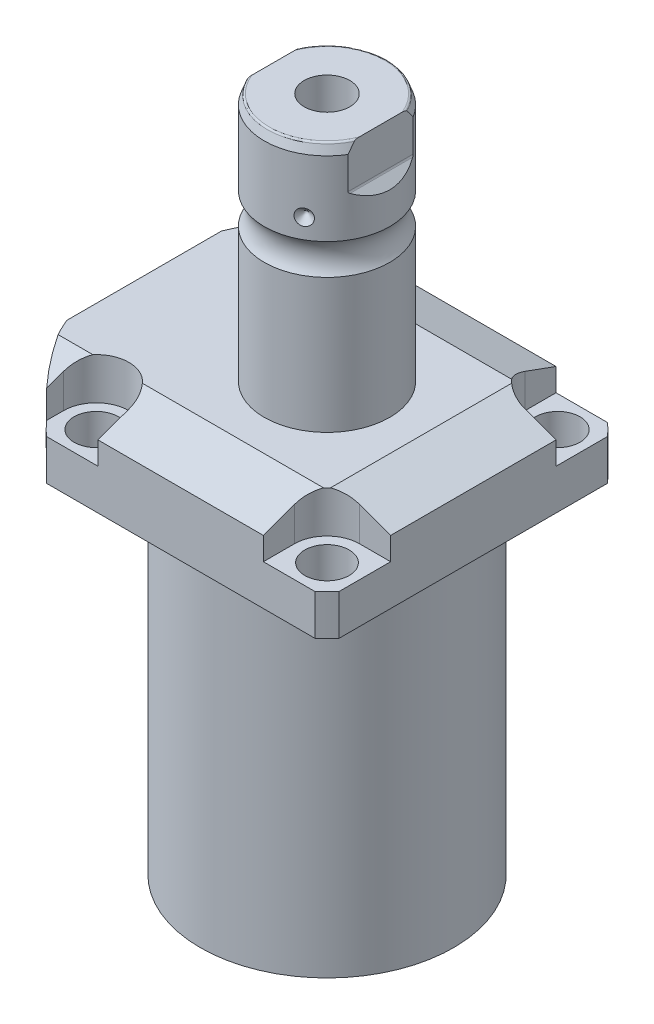
SolidWorks part; units mm, degrees
material "Alloy Steel"
ref_plane "Front Plane" through (0, 0, 0) normal (0, 0, 1) x (1, 0, 0)
ref_plane "Top Plane" through (0, 0, 0) normal (0, 1, 0) x (1, 0, 0)
ref_plane "Right Plane" through (0, 0, 0) normal (1, 0, 0) x (0, 0, -1)
ref_plane "Plane1" through (0, 0, 0) normal (0, 1, 0) x (0, 0, 1)
sketch "Sketch1" plane through (0, 0, 0) normal (0, 1, 0) x (0, 0, 1)
  line L0 (-44.45, 44.45) -> (44.45, 44.45)
  line L1 (44.45, 44.45) -> (44.45, -55.5498)
  line L2 (44.45, -55.5498) -> (-44.45, -55.5498)
  line L3 (-44.45, -55.5498) -> (-44.45, 44.45)
  line L4 (0, 0) -> (0, -60.6467) construction
  dimension "D1" = 55.5498
  dimension "D2" = 99.9998
  dimension "D3" = 88.9
extrude "Extrude1" add sketch "Sketch1" along normal blind 129.794
sketch "Sketch2" plane through (0, 0, 0) normal (0, -1, 0) x (1, 0, 0)
  circle A0 centre (0, 0) radius 60.325
  dimension "D1" = 120.65
extrude "Cut-Extrude1" cut sketch "Sketch2" against normal through all flip side to cut
ref_plane "Plane2" through (0, 0, 0) normal (1, 0, 0) x (0, 0, 1)
sketch "Sketch3" plane through (0, 0, 0) normal (1, 0, 0) x (0, 0, 1)
  line L0 (38.4937, 0) -> (38.4937, -104.775)
  line L1 (38.4937, -104.775) -> (76.5937, -104.775)
  line L2 (76.5937, -104.775) -> (76.5937, 0)
  line L3 (76.5937, 0) -> (38.4937, 0)
  line L4 (0, -93.345) -> (0, 4.445) construction
  line L5 (40.7836, 0) -> (-40.7836, 0) construction
  dimension "D1" = 76.9874
  dimension "D2" = 153.1874
  dimension "D3" = 104.775
revolve "Cut-Revolve1" cut sketch "Sketch3" angle 360 about L4
fillet "Fillet1" radius 0.381 1 edges at (0, 104.775, 38.4937)
sketch "Sketch4" plane through (0, 129.794, 0) normal (0, 1, 0) x (-1, 0, 0)
  line L0 (-44.45, 40.7836) -> (-44.45, -40.7836) construction
  line L1 (40.7836, 44.45) -> (-40.7836, 44.45) construction
  line L2 (-25.1206, -44.45) -> (-25.1206, -35.052)
  line L3 (-44.45, -44.45) -> (-25.1206, -44.45)
  line L4 (-44.45, -25.1206) -> (-44.45, -44.45)
  line L5 (-35.052, -25.1206) -> (-44.45, -25.1206)
  line L6 (44.9834, -44.45) -> (25.1206, -44.45)
  line L7 (25.1206, 44.45) -> (25.1206, 35.052)
  line L8 (44.9834, 44.45) -> (44.9834, 35.052)
  line L9 (44.9834, 44.45) -> (25.1206, 44.45)
  line L10 (-35.052, 25.1206) -> (-44.45, 25.1206)
  line L11 (-44.45, 25.1206) -> (-44.45, 44.45)
  line L12 (-44.45, 44.45) -> (-25.1206, 44.45)
  line L13 (-25.1206, 44.45) -> (-25.1206, 35.052)
  line L14 (-48.9217, 0) -> (49.4551, 0) construction
  line L15 (44.9834, -44.45) -> (44.9834, -35.052)
  line L16 (25.1206, -44.45) -> (25.1206, -35.052)
  arc A0 (25.1206, -35.052) -> (44.9834, -35.052) centre (35.052, -35.052) cw
  arc A1 (-35.052, -25.1206) -> (-25.1206, -35.052) centre (-35.052, -35.052) cw
  arc A2 (-35.052, 25.1206) -> (-25.1206, 35.052) centre (-35.052, 35.052) ccw
  arc A3 (25.1206, 35.052) -> (44.9834, 35.052) centre (35.052, 35.052) ccw
  dimension "D2" = 9.9314
  dimension "D1" = 35.052
  dimension "D3" = 35.052
  dimension "D4" = 35.052
extrude "Cut-Extrude2" cut sketch "Sketch4" against normal blind 12.7
ref_plane "Plane3" through (0, 0, 0) normal (1, 0, 0) x (0, 0, -1)
sketch "Sketch5" plane through (0, 0, 0) normal (1, 0, 0) x (0, 0, -1)
  line L0 (-28.575, 129.794) -> (-44.45, 124.016)
  line L1 (0, 0) -> (0, 154.1081) construction
  line L2 (-28.575, 129.794) -> (-44.45, 129.794)
  line L3 (-44.45, 129.794) -> (-44.45, 124.016)
  dimension "D1" = 15.875
  dimension "D2" = 20
extrude "Cut-Extrude9" cut sketch "Sketch5" against normal through all and the other way through all
mirror "Mirror1" about plane through (0, 0, 0) normal (0, 0, 1) of "Cut-Extrude9"
ref_plane "Plane7" through (0, 0, 0) normal (0, 0, 1) x (1, 0, 0)
sketch "Sketch9" plane through (0, 0, 0) normal (0, 0, 1) x (1, 0, 0)
  line L0 (28.575, 129.794) -> (44.45, 124.016)
  line L1 (44.45, 124.016) -> (44.45, 129.794)
  line L2 (44.45, 129.794) -> (28.575, 129.794)
  dimension "D1" = 15.875
  dimension "D2" = 20
extrude "Cut-Extrude7" cut sketch "Sketch9" against normal through all and the other way through all
ref_plane "Plane8" through (-41.402, 88.9, -18.1102) normal (1, 0, 0) x (0, 1, 0)
sketch "Sketch20" plane through (-41.402, 88.9, -18.1102) normal (1, 0, 0) x (0, 1, 0)
  line L0 (-88.9, 18.1102) -> (39.8401, 18.1102) construction
  line L1 (-7.2797, 36.2204) -> (36.9042, 36.2204) construction
  line L2 (15.875, 41.9227) -> (17.3228, 41.9227)
  line L3 (15.875, 58.8938) -> (15.875, -22.6734) construction
  line L4 (17.3228, 41.9227) -> (17.3228, 39.4716)
  line L5 (17.3228, 39.4716) -> (18.3388, 39.4716)
  line L6 (18.3388, 39.4716) -> (18.3388, 37.465)
  line L7 (18.3388, 37.465) -> (29.3116, 37.465)
  line L8 (29.3116, 37.465) -> (29.3116, 36.2204)
  line L9 (29.3116, 36.2204) -> (15.875, 36.2204)
  line L10 (15.875, 41.9227) -> (15.875, 36.2204)
  dimension "D1" = 18.1102
  dimension "D2" = 11.4046
  dimension "D3" = 1.4478
  dimension "D4" = 6.5024
  dimension "D5" = 1.016
  dimension "D6" = 2.4892
  dimension "D7" = 10.9728
revolve "Cut-Revolve4" cut sketch "Sketch20" angle 360 about L1
mirror "Mirror10" about plane through (0, 0, 0) normal (0, 0, 1) of "Cut-Revolve4"
sketch "Sketch10" plane through (-41.402, 88.9, -18.1102) normal (1, 0, 0) x (0, 1, 0)
  line L0 (-1.0325, 0) -> (1.5659, 0) construction
  line L1 (29.3116, 1.2446) -> (18.3388, 1.2446) construction
  line L2 (18.3388, -1.2446) -> (29.3116, -1.2446) construction
  line L3 (15.875, 58.8938) -> (15.875, -22.6734) construction
  circle A0 centre (16.1417, 4.5212) radius 1.1811
  dimension "D1" = 2.3622
  dimension "D2" = 0.2667
  dimension "D3" = 9.0424
revolve "Revolve4" add sketch "Sketch10" angle 360 about L0
ref_plane "Plane9" through (-41.402, 88.9, 18.1102) normal (1, 0, 0) x (0, 1, 0)
sketch "Sketch11" plane through (-41.402, 88.9, 18.1102) normal (1, 0, 0) x (0, 1, 0)
  line L0 (-1.0325, 0) -> (1.5659, 0) construction
  line L1 (29.3116, 1.2446) -> (18.3388, 1.2446) construction
  line L3 (15.875, 22.6734) -> (15.875, -58.8938) construction
  line L4 (18.3388, -1.2446) -> (29.3116, -1.2446) construction
  circle A0 centre (16.1417, 4.5212) radius 1.1811
  point P10 (0, 0)
  dimension "D1" = 2.3622
  dimension "D2" = 9.0424
  dimension "D3" = 0.2667
revolve "Revolve2" add sketch "Sketch11" angle 360 about L0
ref_plane "Plane10" through (-55.5498, 101.9048, 12.9794) normal (0, 0, 1) x (0, 1, 0)
sketch "S2D0007" plane through (-55.5498, 101.9048, 12.9794) normal (0, 0, 1) x (0, 1, 0)
  line L0 (15.875, 0) -> (26.3525, 0)
  line L1 (26.3525, 0) -> (26.3525, -0.254)
  line L2 (26.3525, -0.254) -> (22.0599, -0.254)
  line L3 (22.0599, -0.254) -> (21.5173, -2.8067)
  line L4 (21.5173, -2.8067) -> (20.8534, -3.4706)
  line L5 (20.8534, -3.4706) -> (20.8534, -14.224)
  line L6 (20.8534, -14.224) -> (15.875, -14.224)
  line L7 (15.875, -14.224) -> (15.875, 0)
  line L8 (15.875, -14.9352) -> (15.875, 0.7112) construction
  line L9 (2.8702, 0) -> (2.8702, -14.7662) construction
  line L10 (27.8892, 0) -> (2.8702, 0) construction
  dimension "D1" = 0.254
  dimension "D2" = 13.0048
  dimension "D3" = 12
  dimension "D4" = 0.254
  dimension "D5" = 20.955
  dimension "D6" = 12.3698
  dimension "D7" = 45
  dimension "D8" = 3.2166
  dimension "D9" = 9.9568
  dimension "D10" = 13.97
revolve "Cut-Revolve2" cut sketch "S2D0007" angle 360 about L8
pattern_linear "LPattern1" count 2 spacing 25.9588 along (0, 0, -1) of "Cut-Revolve2"
ref_plane "Plane12" through (0, 0, 0) normal (1, 0, 0) x (0, -1, 0)
sketch "Sketch15" plane through (0, 0, 0) normal (1, 0, 0) x (0, -1, 0)
  line L0 (-129.794, 0) -> (-129.794, 19.05)
  line L1 (-129.794, 19.05) -> (-170.5783, 19.05)
  line L2 (-179.9925, 19.05) -> (-202.5396, 19.05)
  line L3 (-205.4606, 17.9868) -> (-205.4606, 0)
  line L4 (-205.4606, 0) -> (-129.794, 0)
  line L5 (-197.6361, 0) -> (-64.6704, 0) construction
  line L6 (-129.794, 27.5233) -> (-129.794, -27.5233) construction
  line L7 (-104.775, 40.7836) -> (-104.775, 44.45) construction
  line L8 (-205.4606, 17.9868) -> (-202.5396, 19.05)
  arc A0 (-179.9925, 19.05) -> (-170.5783, 19.05) centre (-175.2854, 25.4254) ccw
  dimension "D2" = 20
  dimension "D4" = 7.9248
  dimension "D6" = 35.0012
  dimension "D1" = 100.6856
  dimension "D3" = 38.1
  dimension "D5" = 30.1752
  dimension "D7" = 2.921
revolve "Revolve3" add sketch "Sketch15" angle 360 about L5
ref_plane "Plane13" through (0, 0, 0) normal (0, 0, -1) x (0, -1, 0)
sketch "Sketch16" plane through (0, 0, 0) normal (0, 0, -1) x (0, -1, 0)
  line L0 (-205.4606, 19.05) -> (-189.6764, 19.05)
  line L1 (-205.4606, -19.05) -> (-205.4606, -16.2814)
  line L2 (-205.4606, 16.2814) -> (-192.7606, 16.2814)
  line L3 (-192.2218, 16.5046) -> (-189.6764, 19.05)
  line L4 (-192.2218, -16.5046) -> (-189.6764, -19.05)
  line L5 (-205.4606, -16.2814) -> (-192.7606, -16.2814)
  line L6 (-205.4606, 19.05) -> (-205.4606, 16.2814)
  line L7 (-205.4606, -19.05) -> (-189.6764, -19.05)
  line L8 (-194.0458, 0) -> (-125.0021, 0) construction
  line L11 (-205.4606, 17.9868) -> (-205.4606, -17.9868) construction
  line L12 (-179.9925, 19.05) -> (-202.5396, 19.05) construction
  arc A0 (-192.7606, 16.2814) -> (-192.2218, 16.5046) centre (-192.7606, 17.0434) ccw
  arc A1 (-192.7606, -16.2814) -> (-192.2218, -16.5046) centre (-192.7606, -17.0434) cw
  point P3 (-192.445, 16.2814)
  dimension "D4" = 0.762
  dimension "D1" = 32.5628
  dimension "D2" = 45
  dimension "D3" = 12.7
extrude "Cut-Extrude8" cut sketch "Sketch16" against normal mid plane 106.68
hole_wizard "Hole1" positions "Sketch18" profile "Sketch17" legacy end condition up to next
sketch "Sketch18" plane through (0, 117.094, 0) normal (0, 1, 0) x (-1, 0, 0)
  arc A0 (44.9834, -35.052) -> (25.1206, -35.052) centre (35.052, -35.052) ccw construction
  arc A1 (25.1206, 35.052) -> (44.9834, 35.052) centre (35.052, 35.052) ccw construction
  arc A2 (-35.052, 25.1206) -> (-25.1206, 35.052) centre (-35.052, 35.052) ccw construction
  arc A3 (-25.1206, -35.052) -> (-35.052, -25.1206) centre (-35.052, -35.052) ccw construction
  point P0 (-35.052, -35.052)
  point P1 (-35.052, 35.052)
  point P3 (35.052, 35.052)
  point P5 (35.052, -35.052)
sketch "Sketch17" plane through (35.052, 117.094, -35.052) normal (1, 0, 0) x (0, 0, 1)
  line L0 (0, 0) -> (0, 12.319)
  line L1 (0, 12.319) -> (6.7437, 12.319)
  line L2 (6.7437, 12.319) -> (6.7437, 0)
  line L3 (6.7437, 0) -> (0, 0)
  line L4 (0, 110) -> (0, -10) construction
  dimension "Diameter" = 13.4874
  dimension "Depth" = 12.319
chamfer "Chamfer1" distance 0.635 angle 45 2 edges at (-41.402, 107.2388, 16.8656) (-41.402, 107.2388, -16.8656)
sketch "Sketch21" plane through (0, 0, 0) normal (0, 0, 1) x (1, 0, 0)
  line L0 (0, 0) -> (0, 194.0957) construction
  line L1 (0, 180.0606) -> (6.9342, 184.2271)
  line L2 (6.9342, 184.2271) -> (6.9342, 205.4606)
  line L4 (6.9342, 205.4606) -> (0, 205.4606)
  line L5 (0, 205.4606) -> (0, 180.0606)
  line L6 (16.2814, 205.4606) -> (-16.2814, 205.4606) construction
  dimension "D1" = 13.8684
  dimension "D2" = 59
  dimension "D3" = 25.4
revolve "Cut-Revolve5" cut sketch "Sketch21" angle 360 about L0
fillet "Fillet2" radius 0.635 2 edges at (0, 205.4606, 17.9868) (0, 205.4606, -17.9868)
sketch "Sketch22" plane through (0, 0, 0) normal (0, 0, 1) x (1, 0, 0)
  line L0 (-37.9974, 185.9534) -> (37.12, 185.9534) construction
  line L1 (-19.05, 188.3664) -> (-16.637, 185.9534)
  line L2 (-16.637, 185.9534) -> (-19.05, 185.9534)
  line L3 (-19.05, 185.9534) -> (-19.05, 188.3664)
  line L4 (-19.05, 189.6764) -> (-19.05, 179.9925) construction
  arc A0 (-19.05, 170.5783) -> (-19.05, 179.9925) centre (-25.4254, 175.2854) ccw construction
  dimension "D2" = 10.668
  dimension "D1" = 4.826
  dimension "D3" = 45
revolve "Cut-Revolve6" cut sketch "Sketch22" angle 360 about L0
pattern_circular "CirPattern1" count 3 over 360 about axis through (0, 197.6361, 0) along (0, 1, 0) of "Cut-Revolve6"
